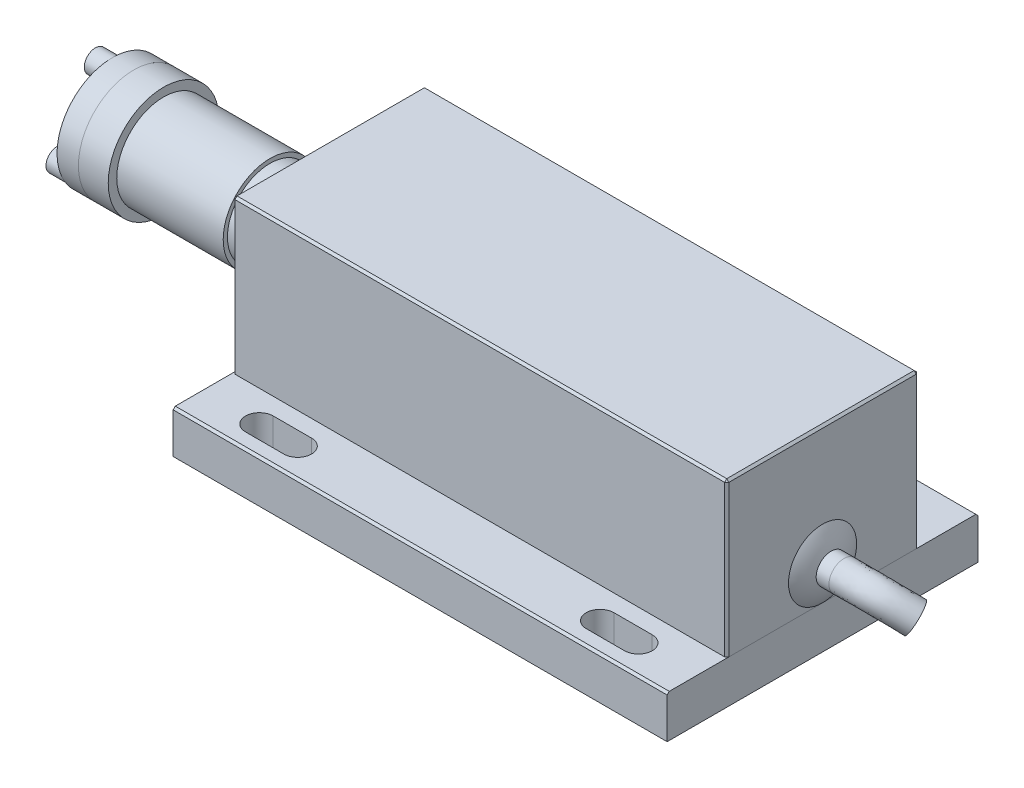
SolidWorks part; units mm, degrees
ref_plane "Front Plane" through (0, 0, 0) normal (0, 0, 1) x (1, 0, 0)
ref_plane "Top Plane" through (0, 0, 0) normal (0, 1, 0) x (1, 0, 0)
ref_plane "Right Plane" through (0, 0, 0) normal (1, 0, 0) x (0, 0, -1)
sketch "Sketch1" plane through (0, 0, 0) normal (0, 1, 0) x (1, 0, 0)
  line L1 (0, 36.5) -> (116, 36.5)
  line L2 (0, 36.5) -> (0, -36.5)
  line L3 (0, -36.5) -> (116, -36.5)
  line L4 (116, 36.5) -> (116, -36.5)
  dimension "D1" = 73
  dimension "D2" = 116
extrude "Boss-Extrude1" add sketch "Sketch1" along normal blind 10
sketch "Sketch2" plane through (0, 10, 0) normal (0, 1, 0) x (1, 0, 0)
  line L0 (0, 36.5) -> (0, -36.5) construction
  line L1 (0, 22.5) -> (116, 22.5)
  line L2 (0, 22.5) -> (0, -22.5)
  line L3 (0, -22.5) -> (116, -22.5)
  line L4 (116, 22.5) -> (116, -22.5)
  line L5 (116, -36.5) -> (116, 36.5) construction
  dimension "D1" = 45
extrude "Boss-Extrude2" add sketch "Sketch2" along normal blind 36 separate body
sketch "Sketch3" plane through (0, 0, 0) normal (-1, 0, 0) x (0, 0, 1)
  line L0 (-36.5, 10) -> (36.5, 10) construction
  circle A0 centre (0, 24.5) radius 14.5
  dimension "D1" = 29
extrude "Boss-Extrude3" add sketch "Sketch3" along normal blind 1
sketch "Sketch4" plane through (-1, 0, 0) normal (-1, 0, 0) x (0, 0, 1)
  circle A0 centre (0, 24.5) radius 10
  circle A1 centre (0, 24.5) radius 14.5 construction
  dimension "D1" = 20
extrude "Boss-Extrude4" add sketch "Sketch4" along normal blind 12.75
sketch "Sketch5" plane through (-13.75, 0, 0) normal (-1, 0, 0) x (0, 0, 1)
  circle A0 centre (0, 24.5) radius 11
  dimension "D1" = 22
extrude "Boss-Extrude5" add sketch "Sketch5" along normal blind 25
sketch "Sketch6" plane through (-38.75, 0, 0) normal (-1, 0, 0) x (0, 0, 1)
  circle A0 centre (0, 24.5) radius 13
  circle A2 centre (0, 24.5) radius 11 construction
  dimension "D1" = 26
extrude "Boss-Extrude6" add sketch "Sketch6" along normal blind 7
sketch "Sketch7" plane through (-45.75, 0, 0) normal (-1, 0, 0) x (0, 0, 1)
  circle A1 centre (0, 24.5) radius 13
  circle A2 centre (0, 24.5) radius 13
  dimension "D1" = 0
extrude "Boss-Extrude7" add sketch "Sketch7" along normal blind 5
sketch "Sketch8" plane through (-50.75, 0, 0) normal (-1, 0, 0) x (0, 0, 1)
  circle A0 centre (0, 24.5) radius 4
  dimension "D1" = 8
extrude "Boss-Extrude8" add sketch "Sketch8" along normal blind 5
sketch "Sketch9" plane through (0, 10, 0) normal (0, 1, 0) x (1, 0, 0)
  line L0 (13.5, 29.75) -> (22.5, 29.75) construction
  line L1 (13.5, 33) -> (22.5, 33)
  line L2 (13.5, 26.5) -> (22.5, 26.5)
  line L3 (93.5, 29.75) -> (102.5, 29.75) construction
  line L4 (93.5, 33) -> (102.5, 33)
  line L5 (93.5, 26.5) -> (102.5, 26.5)
  line L6 (0, 0) -> (116, 0) construction
  line L7 (116, -22.5) -> (116, 22.5) construction
  line L8 (116, 36.5) -> (0, 36.5) construction
  line L10 (0, 36.5) -> (0, 0) construction
  line L11 (116, -36.5) -> (116, 36.5) construction
  line L12 (13.5, -29.75) -> (22.5, -29.75) construction
  line L13 (13.5, -33) -> (22.5, -33)
  line L14 (13.5, -26.5) -> (22.5, -26.5)
  line L15 (93.5, -29.75) -> (102.5, -29.75) construction
  line L16 (93.5, -33) -> (102.5, -33)
  line L17 (93.5, -26.5) -> (102.5, -26.5)
  arc A0 (13.5, 33) -> (13.5, 26.5) centre (13.5, 29.75) ccw
  arc A1 (22.5, 26.5) -> (22.5, 33) centre (22.5, 29.75) ccw
  arc A2 (93.5, 33) -> (93.5, 26.5) centre (93.5, 29.75) ccw
  arc A3 (102.5, 26.5) -> (102.5, 33) centre (102.5, 29.75) ccw
  arc A4 (13.5, -33) -> (13.5, -26.5) centre (13.5, -29.75) cw
  arc A5 (22.5, -26.5) -> (22.5, -33) centre (22.5, -29.75) cw
  arc A6 (93.5, -33) -> (93.5, -26.5) centre (93.5, -29.75) cw
  arc A7 (102.5, -26.5) -> (102.5, -33) centre (102.5, -29.75) cw
  point P2 (18, 29.75)
  point P7 (98, 29.75)
  point P28 (18, -29.75)
  point P35 (98, -29.75)
  dimension "D1" = 6.5
  dimension "D2" = 3.5
  dimension "D3" = 9
  dimension "D4" = 13.5
  dimension "D5" = 13.5
extrude "Cut-Extrude1" cut sketch "Sketch9" against normal up to next (10 mm away)
chamfer "Chamfer1" distance 0.5 angle 45 2 edges at (58, 10, 36.5) (58, 10, -36.5)
chamfer "Chamfer2" distance 0.5 angle 45 8 edges at (116, 28, 22.5) (116, 28, -22.5) (116, 46, 0) (0, 28, -22.5) (0, 28, 22.5) (58, 46, 22.5) (0, 46, 0) (58, 46, -22.5)
sketch3d "3DSketch1"
  line L0 (116, 18, 0) -> (121, 18, 0)
  line L1 (116, 18, 0) -> (116, 10, 0) construction
  line L2 (116, 10, 22) -> (116, 10, -22) construction
  spline S0 degree 3 poles (121, 18, 0) (128.3987, 18, 0) (128.2492, 18.8942, 0.8654) (134.4491, 14.5082, -3.3792) knots 0 0 0 0 1 1 1 1
  dimension "D1" = 5
  dimension "D2" = 8
sketch "Sketch10" plane through (116, 0, 0) normal (1, 0, 0) x (0, 0, -1)
  circle A0 centre (0, 18) radius 3.5
  dimension "D1" = 7
sweep "Sweep1" add profiles "Sketch10" path "3DSketch1"
ref_plane "Plane1" through (0, 0, 0) normal (0, 0, -1) x (-1, 0, 0)
sketch "Sketch11" plane through (0, 0, 0) normal (0, 0, -1) x (-1, 0, 0)
  line L0 (-116, 18) -> (-116, 26)
  line L1 (-116, 21.5) -> (-116, 14.5) construction
  line L2 (-116, 10) -> (-116, 45.5) construction
  line L3 (-116, 18) -> (-118.4327, 18)
  line L4 (-118.4327, 18) -> (-118.4327, 26) construction
  line L5 (-118.4327, 26) -> (-116, 26) construction
  line L6 (-118, 21.5) -> (-116, 21.5) construction
  line L7 (-116, 21.5) -> (-121, 21.5) construction
  line L8 (-116, 21.5) -> (-121, 21.5) construction
  arc A0 (-118.4327, 18) -> (-116, 26) centre (-104.0625, 18) cw
  dimension "D1" = 8
  dimension "D2" = 2
revolve "Revolve1" add sketch "Sketch11" angle 360 about L0
sketch "Sketch13" plane through (-50.75, 0, 0) normal (-1, 0, 0) x (0, 0, 1)
  circle A0 centre (0, 34.875) radius 2.625
  circle A1 centre (8.985, 19.3125) radius 2.625
  circle A2 centre (-8.985, 19.3125) radius 2.625
  circle A3 centre (0, 24.5) radius 10.375 construction
  circle A4 centre (0, 24.5) radius 4 construction
  circle A5 centre (0, 24.5) radius 13 construction
  dimension "D1" = 5.25
  dimension "D2" = 120
  dimension "D3" = 120
extrude "Boss-Extrude9" add sketch "Sketch13" along normal blind 4
sketch "Sketch14" plane through (-54.75, 0, 0) normal (-1, 0, 0) x (0, 0, 1)
  line L0 (-1.75, 35.8854) -> (0, 36.8957)
  line L1 (0, 36.8957) -> (1.75, 35.8854)
  line L2 (1.75, 35.8854) -> (1.75, 33.8646)
  line L3 (1.75, 33.8646) -> (0, 32.8543)
  line L4 (0, 32.8543) -> (-1.75, 33.8646)
  line L5 (-1.75, 33.8646) -> (-1.75, 35.8854)
  line L6 (0, 36.8957) -> (0, 32.8543) construction
  line L7 (-1.75, 35.8854) -> (1.75, 33.8646) construction
  line L8 (-1.75, 33.8646) -> (1.75, 35.8854) construction
  line L9 (-7.235, 18.3021) -> (-8.985, 17.2918)
  line L10 (-8.985, 17.2918) -> (-10.735, 18.3021)
  line L11 (-10.735, 18.3021) -> (-10.735, 20.3229)
  line L12 (-10.735, 20.3229) -> (-8.985, 21.3332)
  line L13 (-8.985, 21.3332) -> (-7.235, 20.3229)
  line L14 (-7.235, 20.3229) -> (-7.235, 18.3021)
  line L15 (8.985, 21.3332) -> (10.735, 20.3229)
  line L16 (10.735, 20.3229) -> (10.735, 18.3021)
  line L17 (10.735, 18.3021) -> (8.985, 17.2918)
  line L18 (8.985, 17.2918) -> (7.235, 18.3021)
  line L19 (7.235, 18.3021) -> (7.235, 20.3229)
  line L20 (7.235, 20.3229) -> (8.985, 21.3332)
  circle A0 centre (0, 34.875) radius 2.625 construction
  point P7 (0, 34.875)
  point P12 (0, 24.5)
  point P27 (0, 24.5)
  dimension "D1" = 3.5
  dimension "D2" = 3
extrude "Cut-Extrude2" cut sketch "Sketch14" against normal blind 3
